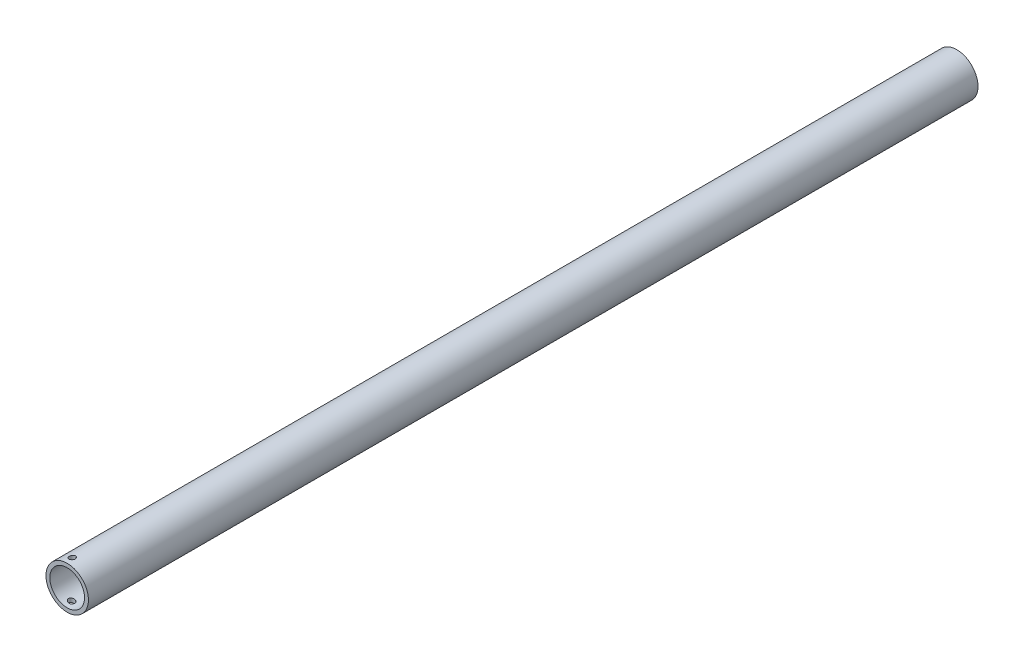
SolidWorks part; units mm, degrees
ref_plane "Front" through (0, 0, 0) normal (0, 0, 1) x (1, 0, 0)
ref_plane "Top" through (0, 0, 0) normal (0, 1, 0) x (1, 0, 0)
ref_plane "Right" through (0, 0, 0) normal (1, 0, 0) x (0, 0, -1)
sketch "草图1" plane through (0, 0, 0) normal (0, 0, 1) x (1, 0, 0)
  circle A0 centre (0, 0) radius 9
  circle A1 centre (0, 0) radius 11
  dimension "D1" = 22
  dimension "D2" = 18
extrude "凸台-拉伸1" add sketch "草图1" along normal blind 461 contours A1 | A0
ref_plane "基准面1" through (0.1547, 10.9989, 0) normal (0.0141, 0.9999, 0) x (0, 0, 1)
sketch "草图2" plane through (0.1547, 10.9989, 0) normal (0.0141, 0.9999, 0) x (0, 0, 1)
  line L0 (461, -11) -> (461, 11) construction
  circle A0 centre (457, -1.5623) radius 1.6
  dimension "D1" = 3.2
  dimension "D2" = 4
extrude "切除-拉伸1" cut sketch "草图2" against normal through all
